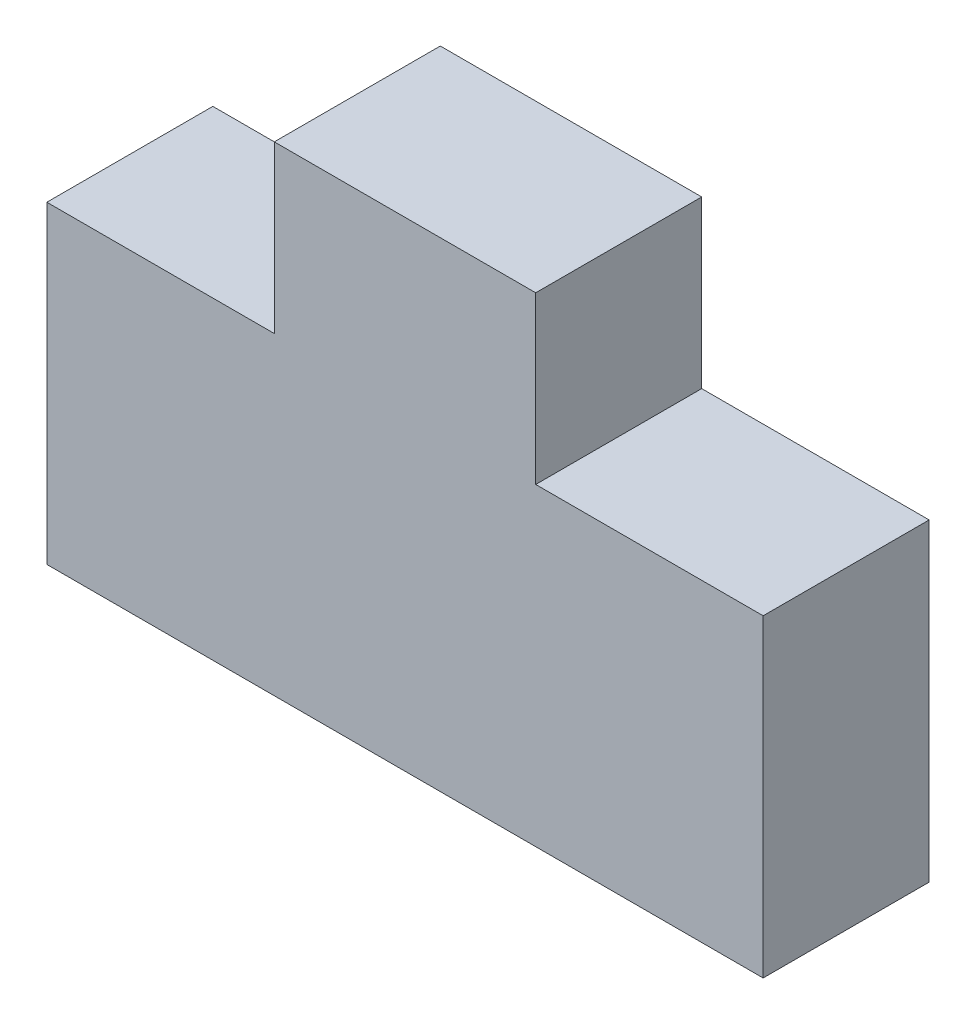
SolidWorks part; units mm, degrees
ref_plane "Front Plane" through (0, 0, 0) normal (0, 0, 1) x (1, 0, 0)
ref_plane "Top Plane" through (0, 0, 0) normal (0, 1, 0) x (1, 0, 0)
ref_plane "Right Plane" through (0, 0, 0) normal (1, 0, 0) x (0, 0, -1)
sketch "Sketch1" plane through (0, 0, 0) normal (0, 1, 0) x (1, 0, 0)
  line L1 (0, 0) -> (27.4, 0)
  line L2 (0, 0) -> (0, 6.35)
  line L3 (0, 6.35) -> (27.4, 6.35)
  line L4 (27.4, 0) -> (27.4, 6.35)
  dimension "D1" = 27.4
  dimension "D2" = 6.35
extrude "Boss-Extrude1" add sketch "Sketch1" along normal blind 12
sketch "Sketch2" plane through (0, 0, 0) normal (0, 0, 1) x (1, 0, 0)
  line L0 (13.7, 12) -> (13.7, 0) construction
  line L1 (0, 12) -> (27.4, 12) construction
  line L2 (0, 0) -> (27.4, 0) construction
  line L3 (13.7, 12) -> (13.7, 18.35) construction
  line L4 (8.7, 12) -> (18.7, 12)
  line L5 (8.7, 12) -> (8.7, 18.35)
  line L6 (8.7, 18.35) -> (18.7, 18.35)
  line L7 (18.7, 12) -> (18.7, 18.35)
  dimension "D1" = 10
  dimension "D2" = 6.35
extrude "Boss-Extrude2" add sketch "Sketch2" against normal up to vertex (6.35 mm away)
